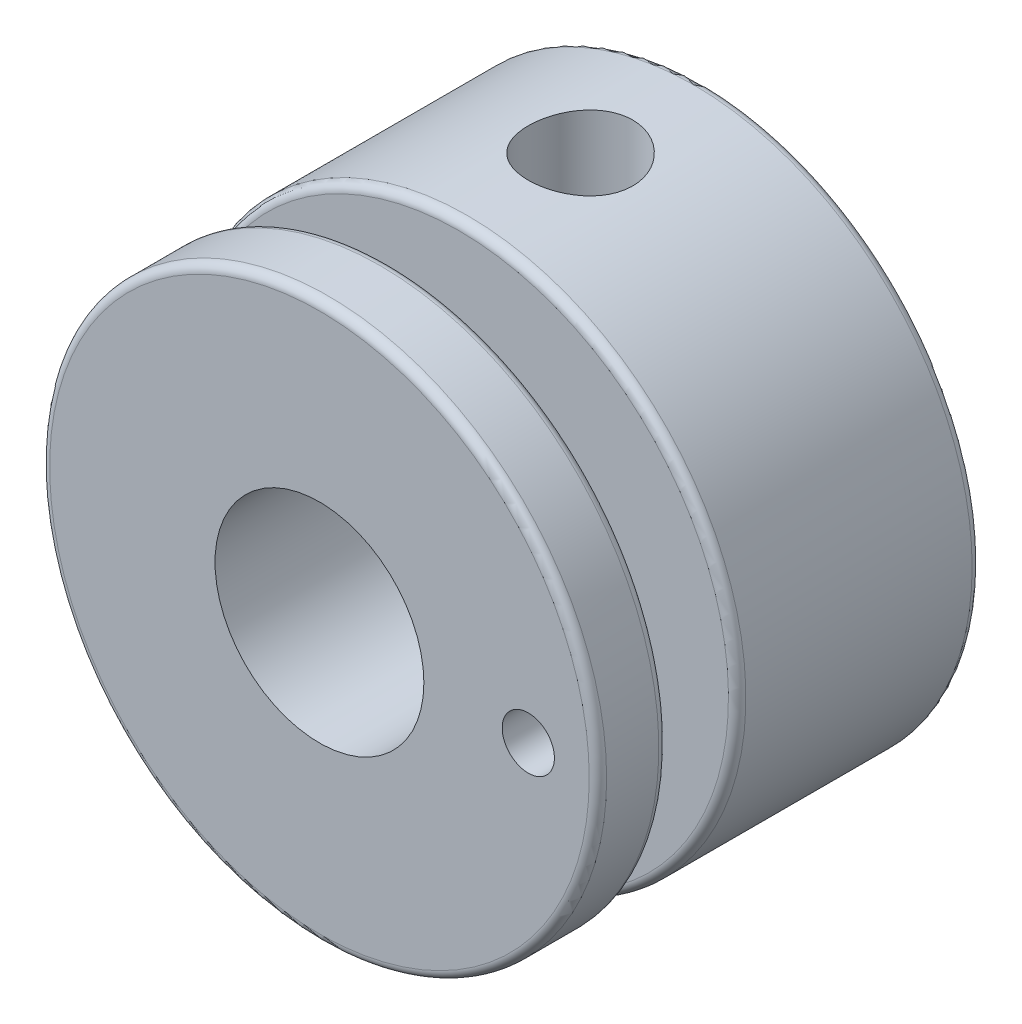
SolidWorks part; units mm, degrees
ref_plane "Front Plane" through (0, 0, 0) normal (0, 0, 1) x (1, 0, 0)
ref_plane "Top Plane" through (0, 0, 0) normal (0, 1, 0) x (1, 0, 0)
ref_plane "Right Plane" through (0, 0, 0) normal (1, 0, 0) x (0, 0, -1)
sketch "Sketch1" plane through (0, 0, 0) normal (0, 0, 1) x (1, 0, 0)
  circle A0 centre (0, 0) radius 8
  dimension "D1" = 16
extrude "Boss-Extrude1" add sketch "Sketch1" along normal blind 11 contours A0
sketch "Sketch2" plane through (0, 0, 0) normal (1, 0, 0) x (0, 0, -1)
  line L0 (0, 8) -> (-11, 8) construction
  line L1 (-9, 8) -> (-7, 8)
  line L2 (-9, 8) -> (-9, 5)
  line L3 (-9, 5) -> (-7, 5)
  line L4 (-7, 8) -> (-7, 5)
  line L5 (-11, 8) -> (-11, -8) construction
  dimension "D1" = 3
  dimension "D2" = 0
  dimension "D3" = 2
  dimension "D4" = 2
sketch "Sketch3" plane through (0, 0, 0) normal (1, 0, 0) x (0, 0, -1)
  line L0 (5.2495, 0) -> (-14.7505, 0)
  dimension "D1" = 20
revolve "Cut-Revolve2" cut sketch "Sketch2" angle 360 about L0
sketch "Sketch5" plane through (0, 0, 0) normal (0, 1, 0) x (1, 0, 0)
  line L1 (0, 5.2495) -> (0, -14.7505) construction
  line L2 (8, 0) -> (-8, 0) construction
  circle A1 centre (0, -3.5) radius 1.5
  dimension "D1" = 3
  dimension "D2" = 3.5
extrude "Cut-Extrude1" cut sketch "Sketch5" along normal up to next from offset 2.5 contours A1
sketch "Sketch6" plane through (0, 0, 0) normal (0, 0, 1) x (1, 0, 0)
  circle A0 centre (0, 0) radius 3
  dimension "D1" = 6
extrude "Cut-Extrude2" cut sketch "Sketch6" along normal up to next
fillet "Fillet3" radius 0.25 1 edges at (0, 8, 9)
fillet "Fillet4" radius 0.25 1 edges at (0, 8, 7)
fillet "Fillet5" radius 0.25 2 edges at (8, 0, 0) (8, 0, 11)
sketch "Sketch7" plane through (0, 0, 11) normal (0, 0, 1) x (1, 0, 0)
  line L0 (-7.75, 0) -> (7.75, 0) construction
  circle A0 centre (0, 0) radius 7.75 construction
  circle A1 centre (6, 0) radius 0.75
  dimension "D1" = 1.5
  dimension "D2" = 1.75
extrude "Cut-Extrude3" cut sketch "Sketch7" against normal up to next
